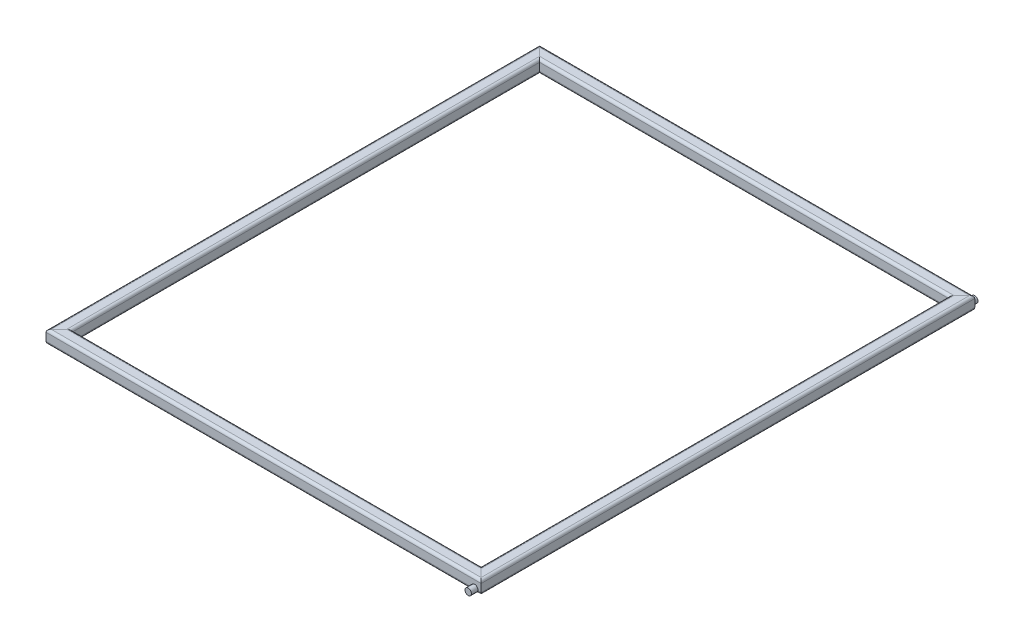
SolidWorks part; units mm, degrees
ref_plane "Front Plane" through (0, 0, 0) normal (0, 0, 1) x (1, 0, 0)
ref_plane "Top Plane" through (0, 0, 0) normal (0, 1, 0) x (1, 0, 0)
ref_plane "Right Plane" through (0, 0, 0) normal (1, 0, 0) x (0, 0, -1)
sketch "Sketch1" plane through (0, 0, 0) normal (0, 1, 0) x (1, 0, 0)
  line L1 (325, -370) -> (-325, -370)
  line L2 (325, -370) -> (325, 370)
  line L3 (325, 370) -> (-325, 370)
  line L4 (-325, -370) -> (-325, 370)
  line L5 (325, -370) -> (-325, 370) construction
  line L6 (325, 370) -> (-325, -370) construction
  point P0 (0, 0)
  dimension "D1" = 650
  dimension "D2" = 740
other "Square tube - configured 20 X 20 X 2(1)"
ref_plane "Plane1" through (-325, 0, 370) normal (0, 0, -1) x (-1, 0, 0)
sketch "Sketch12" plane through (-325, 0, 370) normal (0, 0, -1) x (-1, 0, 0)
  line L0 (-6, -8) -> (6, -8)
  line L1 (-8, -6) -> (-8, 6)
  line L2 (6, 8) -> (-6, 8)
  line L3 (8, 6) -> (8, -6)
  line L4 (-6, -10) -> (6, -10)
  line L5 (-10, -6) -> (-10, 6)
  line L6 (6, 10) -> (-6, 10)
  line L7 (10, 6) -> (10, -6)
  arc A0 (10, 6) -> (6, 10) centre (6, 6) ccw
  arc A1 (6, -10) -> (10, -6) centre (6, -6) ccw
  arc A2 (-10, -6) -> (-6, -10) centre (-6, -6) ccw
  arc A3 (-6, 10) -> (-10, 6) centre (-6, 6) ccw
  arc A4 (-6, 8) -> (-8, 6) centre (-6, 6) ccw
  arc A5 (8, 6) -> (6, 8) centre (6, 6) ccw
  arc A6 (6, -8) -> (8, -6) centre (6, -6) ccw
  arc A7 (-8, -6) -> (-6, -8) centre (-6, -6) ccw
  point P0 (-10, 0)
  point P1 (10, 0)
  point P2 (0, 10)
  point P3 (0, -10)
  point P4 (0, 0)
  point P5 (-10, -10)
  point P6 (10, -10)
  point P7 (10, 10)
  point P8 (-10, 10)
  point P33 (0, 0)
  dimension "D1" = 4
  dimension "Thickness" = 2
  dimension "V_leg" = 20
sketch "Sketch13" plane through (0, 0, 380) normal (0, 0, 1) x (1, 0, 0)
  line L2 (-331, -10) -> (331, -10) construction
  line L3 (335, 6) -> (335, -6) construction
  circle A0 centre (325, -5) radius 5
  dimension "D1" = 10
  dimension "D2" = 10
extrude "Boss-Extrude1" add sketch "Sketch13" along normal blind 10 and the other way up to next separate body
mirror "Mirror2" about plane through (0, 0, 0) normal (0, 0, 1) of "Boss-Extrude1"
